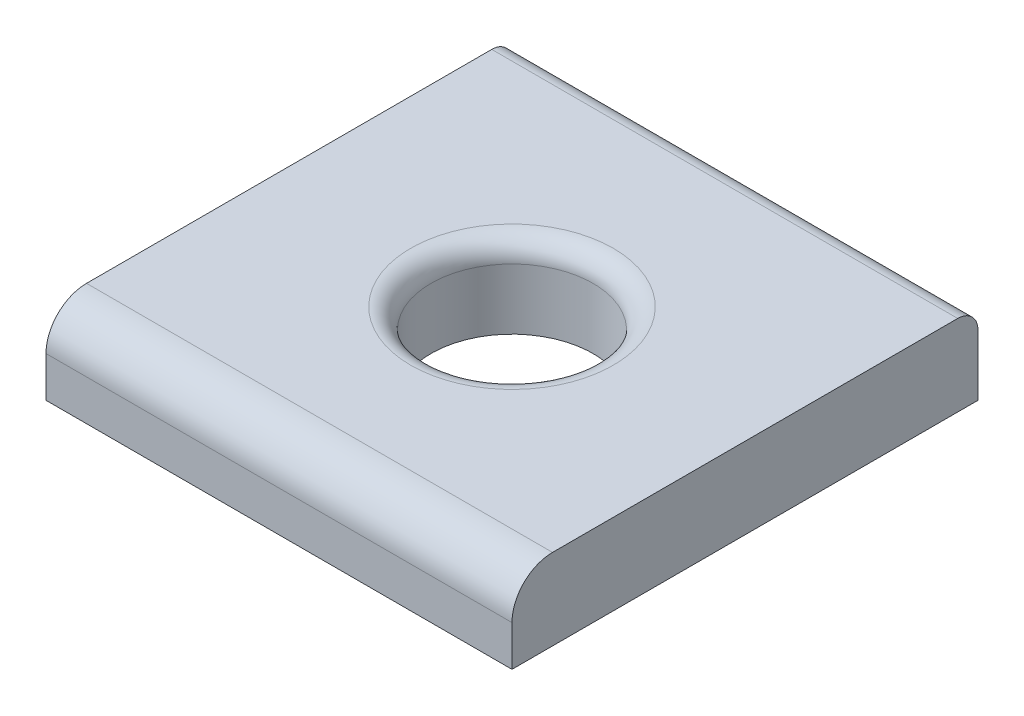
SolidWorks part; units mm, degrees
material "1060 Alloy"
ref_plane "Front Plane" through (0, 0, 0) normal (0, 0, 1) x (1, 0, 0)
ref_plane "Top Plane" through (0, 0, 0) normal (0, 1, 0) x (1, 0, 0)
ref_plane "Right Plane" through (0, 0, 0) normal (1, 0, 0) x (0, 0, -1)
sketch "Sketch1" plane through (0, 0, 0) normal (0, 1, 0) x (1, 0, 0)
  line L1 (-5.75, 5.75) -> (5.75, 5.75)
  line L2 (-5.75, 5.75) -> (-5.75, -5.75)
  line L3 (-5.75, -5.75) -> (5.75, -5.75)
  line L4 (5.75, 5.75) -> (5.75, -5.75)
  line L5 (-5.75, 5.75) -> (5.75, -5.75) construction
  line L6 (-5.75, -5.75) -> (5.75, 5.75) construction
  point P0 (0, 0)
  dimension "D1" = 11.5
  dimension "D2" = 11.5
extrude "Boss-Extrude1" add sketch "Sketch1" along normal blind 2
sketch "Sketch2" plane through (0, 2, 0) normal (0, 1, 0) x (1, 0, 0)
  circle A0 centre (0, 0) radius 2
  dimension "D1" = 4
extrude "Cut-Extrude1" cut sketch "Sketch2" against normal through all
fillet "Fillet1" radius 1 1 edges at (0, 2, 5.75)
fillet "Fillet2" radius 0.5 1 edges at (0, 2, -5.75)
fillet "Fillet3" radius 0.5 1 edges at (0, 2, 2)
